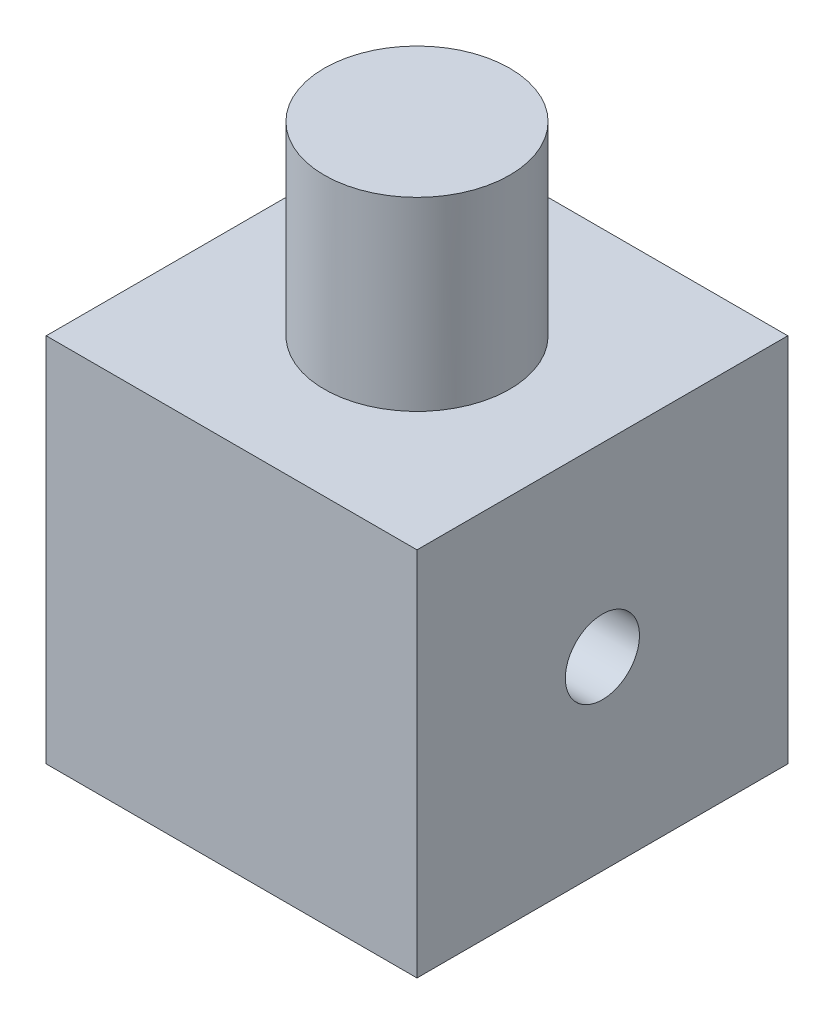
SolidWorks part; units mm, degrees
ref_plane "Front Plane" through (0, 0, 0) normal (0, 0, 1) x (1, 0, 0)
ref_plane "Top Plane" through (0, 0, 0) normal (0, 1, 0) x (1, 0, 0)
ref_plane "Right Plane" through (0, 0, 0) normal (1, 0, 0) x (0, 0, -1)
sketch "Sketch1" plane through (0, 0, 0) normal (0, 1, 0) x (1, 0, 0)
  line L1 (-14.6482, 16.7908) -> (-4.6482, 16.7908)
  line L2 (-14.6482, 16.7908) -> (-14.6482, 26.7908)
  line L3 (-14.6482, 26.7908) -> (-4.6482, 26.7908)
  line L4 (-4.6482, 16.7908) -> (-4.6482, 26.7908)
  dimension "D1" = 10
  dimension "D2" = 10
extrude "Boss-Extrude1" add sketch "Sketch1" along normal blind 10
ref_plane "Plane1" through (0, 10, 0) normal (0, 1, 0) x (1, 0, 0)
sketch "Sketch2" plane through (0, 10, 0) normal (0, 1, 0) x (1, 0, 0)
  line L0 (-4.6482, 26.7908) -> (-14.6482, 26.7908) construction
  line L1 (-4.6482, 16.7908) -> (-4.6482, 26.7908) construction
  line L2 (-14.6482, 16.7908) -> (-4.6482, 16.7908) construction
  circle A0 centre (-9.6482, 21.7908) radius 2.5
  point P0 (-9.6482, 26.7908)
  point P1 (-9.6482, 21.7908)
  dimension "D1" = 5
  dimension "D2" = 5
extrude "Boss-Extrude2" add sketch "Sketch2" along normal blind 5
ref_plane "Plane2" through (-14.6482, 0, 0) normal (-1, 0, 0) x (0, 0, 1)
sketch "Sketch3" plane through (-14.6482, 0, 0) normal (-1, 0, 0) x (0, 0, 1)
  circle A0 centre (-21.7908, 5) radius 1
  point P0 (-21.7908, 5)
  dimension "D1" = 2
extrude "Cut-Extrude1" cut sketch "Sketch3" against normal blind 10
ref_plane "Plane3" through (0, 0, 0) normal (0, -1, 0) x (-1, 0, 0)
sketch "Sketch4" plane through (0, 0, 0) normal (0, -1, 0) x (-1, 0, 0)
  circle A0 centre (9.6482, 21.7908) radius 0.5
  point P0 (9.6482, 21.7908)
extrude "Cut-Extrude2" cut sketch "Sketch4" against normal blind 5
